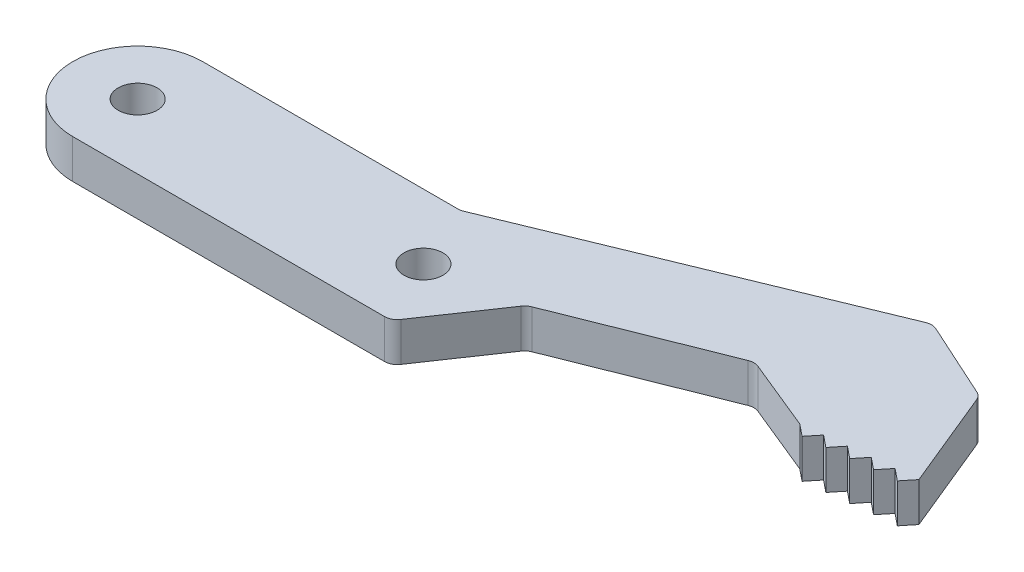
SolidWorks part; units mm, degrees
ref_plane "Front Plane" through (0, 0, 0) normal (0, 0, 1) x (1, 0, 0)
ref_plane "Top Plane" through (0, 0, 0) normal (0, 1, 0) x (1, 0, 0)
ref_plane "Right Plane" through (0, 0, 0) normal (1, 0, 0) x (0, 0, -1)
sketch "Sketch1" plane through (0, 0, 0) normal (0, 1, 0) x (1, 0, 0)
  line L1 (0, -5) -> (23.9989, -5)
  line L2 (0, 5) -> (19.6524, 5)
  line L3 (20.0327, 5.0751) -> (45.2294, 15.4347)
  line L4 (46.0242, 15.4199) -> (51.8314, 12.7746)
  line L5 (52.3417, 12.2448) -> (55.4426, 4.7029)
  line L6 (24.8266, -4.5611) -> (28.5649, 0.9541)
  line L7 (29.0223, 1.322) -> (40.9296, 6.07)
  line L8 (41.6788, 6.0666) -> (47.1446, 3.8294)
  line L11 (47.1446, 3.8294) -> (48.0617, 3.087)
  line L12 (48.0617, 3.087) -> (48.8042, 4.0041)
  line L13 (48.8042, 4.0041) -> (49.7213, 3.2617)
  line L14 (49.7213, 3.2617) -> (50.4638, 4.1788)
  line L15 (50.4638, 4.1788) -> (51.3809, 3.4364)
  line L16 (51.3809, 3.4364) -> (52.1234, 4.3535)
  line L17 (52.1234, 4.3535) -> (53.0405, 3.6111)
  line L18 (53.0405, 3.6111) -> (53.783, 4.5282)
  line L19 (53.783, 4.5282) -> (54.7001, 3.7858)
  line L20 (54.7001, 3.7858) -> (55.4426, 4.7029)
  circle A0 centre (0, 0) radius 1.5
  arc A1 (0, 5) -> (0, -5) centre (0, 0) ccw
  circle A2 centre (22, 0) radius 1.5
  arc A3 (28.5649, 0.9541) -> (29.0223, 1.322) centre (29.3927, 0.3931) cw
  arc A4 (40.9296, 6.07) -> (41.6788, 6.0666) centre (41.2999, 5.1412) cw
  arc A5 (51.8314, 12.7746) -> (52.3417, 12.2448) centre (51.4169, 11.8646) cw
  arc A6 (45.2294, 15.4347) -> (46.0242, 15.4199) centre (45.6096, 14.5098) cw
  arc A7 (19.6524, 5) -> (20.0327, 5.0751) centre (19.6524, 6) ccw
  arc A8 (23.9989, -5) -> (24.8266, -4.5611) centre (23.9989, -4) ccw
  point P27 (28.7372, 1.2083)
  point P30 (41.3048, 6.2197)
  point P33 (52.1913, 12.6106)
  point P36 (45.63, 15.5994)
  point P39 (19.85, 5)
  point P42 (24.5291, -5)
  dimension "D1" = 3
  dimension "D2" = 10
  dimension "D4" = 3
  dimension "D20" = 1
  dimension "D3" = 22
  dimension "D5" = 124.13
  dimension "D6" = 7.5
  dimension "D7" = 214.13
  dimension "D8" = 13.53
  dimension "D9" = 224
  dimension "D10" = 6.31
  dimension "D11" = 157.65
  dimension "D12" = 19.85
  dimension "D13" = 25.78
  dimension "D14" = 7.21
  dimension "D15" = 133.16
  dimension "D16" = 136.84
  dimension "D17" = 8.55
  dimension "D18" = 1.18
  dimension "D19" = 1.18
extrude "Boss-Extrude1" add sketch "Sketch1" along normal blind 3
